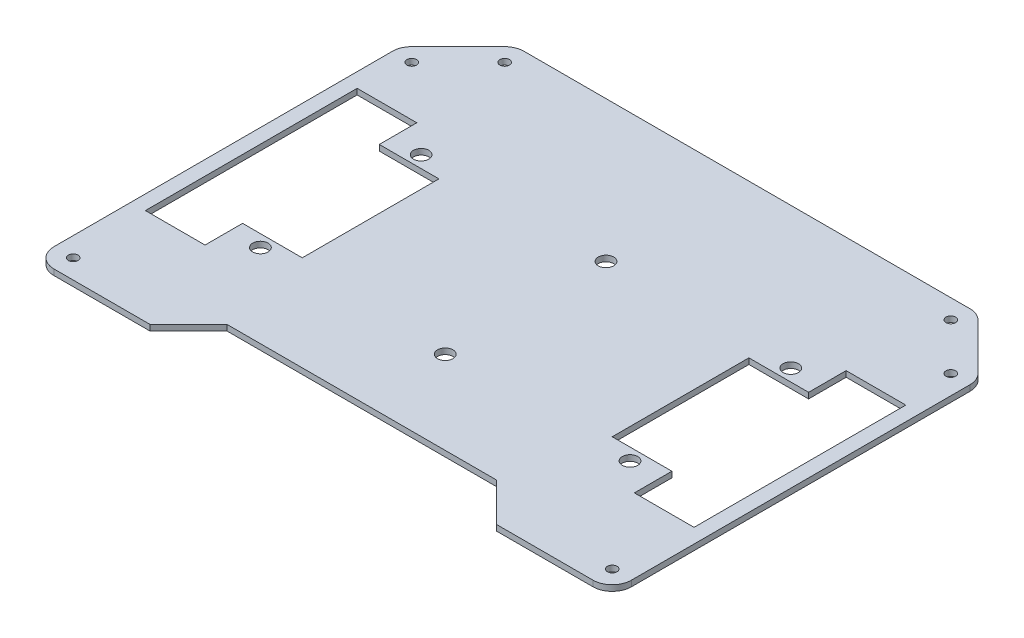
SolidWorks part; units mm, degrees
ref_plane "Face" through (0, 0, 0) normal (0, 0, 1) x (1, 0, 0)
ref_plane "Dessus" through (0, 0, 0) normal (0, 1, 0) x (1, 0, 0)
ref_plane "Droite" through (0, 0, 0) normal (1, 0, 0) x (0, 0, -1)
sketch "Esquisse1" plane through (0, 0, 0) normal (0, 1, 0) x (1, 0, 0)
  line L0 (-150, -105) -> (150, -105)
  line L1 (-150, 0) -> (-150, -105)
  line L2 (0, 115) -> (0, -105) construction
  line L3 (-150, 0) -> (-150, 85)
  line L4 (-150, 85) -> (-120, 115)
  line L5 (-120, 115) -> (120, 115)
  line L6 (150, 0) -> (150, -105)
  line L7 (-142.5, 55) -> (-142.5, -55)
  line L8 (-111.5, -55) -> (-142.5, -55)
  line L9 (-111.5, -35.5) -> (-111.5, -55)
  line L10 (-80.5, -35.5) -> (-111.5, -35.5)
  line L11 (-80.5, -35.5) -> (-80.5, 35.5)
  line L12 (-80.5, 35.5) -> (-111.5, 35.5)
  line L13 (-111.5, 35.5) -> (-111.5, 55)
  line L14 (-111.5, 55) -> (-142.5, 55)
  line L15 (111.5, 55) -> (142.5, 55)
  line L16 (-150, 0) -> (150, 0) construction
  line L17 (111.5, 35.5) -> (111.5, 55)
  line L18 (80.5, 35.5) -> (111.5, 35.5)
  line L19 (80.5, -35.5) -> (80.5, 35.5)
  line L20 (80.5, -35.5) -> (111.5, -35.5)
  line L21 (111.5, -35.5) -> (111.5, -55)
  line L22 (111.5, -55) -> (142.5, -55)
  line L23 (142.5, 55) -> (142.5, -55)
  line L24 (150, 85) -> (120, 115)
  line L25 (150, 0) -> (150, 85)
  line L26 (-96, 41.75) -> (0, 41.75) construction
  circle A0 centre (0, 41.75) radius 4
  circle A1 centre (-96, 41.75) radius 4
  circle A2 centre (0, -41.75) radius 4
  circle A3 centre (-96, -41.75) radius 4
  circle A4 centre (96, -41.75) radius 4
  circle A5 centre (96, 41.75) radius 4
  point P2 (0, 0)
  point P15 (-142.5, 0)
  point P22 (-80.5, 0)
  point P30 (80.5, 0)
  point P31 (142.5, 0)
  dimension "D12" = 8
  dimension "D2" = 50
  dimension "D3" = 45
  dimension "D4" = 110
  dimension "D5" = 31
  dimension "D6" = 71
  dimension "D7" = 161
  dimension "D8" = 285
  dimension "D9" = 30
  dimension "D10" = 220
  dimension "D11" = 300
  dimension "D13" = 96
  dimension "D14" = 41.75
extrude "Extrusion1" add sketch "Esquisse1" along normal blind 3
fillet "Congé2" radius 10 6 edges at (-150, 1.5, -85) (-120, 1.5, -115) (120, 1.5, -115) (150, 1.5, -85) (150, 1.5, 105) (-150, 1.5, 105)
sketch "Esquisse3" plane through (0, 3, 0) normal (0, 1, 0) x (1, 0, 0)
  line L3 (0, -105) -> (0, 115) construction
  line L4 (-140, -105) -> (140, -105) construction
  line L5 (115.8579, 115) -> (-115.8579, 115) construction
  circle A0 centre (-140, -95) radius 2.5
  circle A1 centre (-140, 80.8579) radius 2.5
  circle A2 centre (-115.8579, 105) radius 2.5
  circle A3 centre (140, -95) radius 2.5
  circle A4 centre (140, 80.8579) radius 2.5
  circle A5 centre (115.8579, 105) radius 2.5
  arc A6 (-150, -95) -> (-140, -105) centre (-140, -95) ccw construction
  arc A7 (-147.0711, 87.9289) -> (-150, 80.8579) centre (-140, 80.8579) ccw construction
  arc A8 (-115.8579, 115) -> (-122.9289, 112.0711) centre (-115.8579, 105) ccw construction
  dimension "D2" = 5
extrude "Extrusion2" cut sketch "Esquisse3" against normal up to next
sketch "Esquisse4" plane through (0, 3, 0) normal (0, 1, 0) x (1, 0, 0)
  line L0 (0, -105) -> (0, 115) construction
  line L1 (-140, -105) -> (140, -105) construction
  line L2 (115.8579, 115) -> (-115.8579, 115) construction
  line L3 (-90, -105) -> (-70, -85)
  line L4 (-70, -85) -> (70, -85)
  line L5 (-90, -105) -> (90, -105)
  line L6 (90, -105) -> (70, -85)
  point P10 (0, -85)
  dimension "D1" = 45
  dimension "D2" = 70
  dimension "D3" = 20
extrude "Extrusion3" cut sketch "Esquisse4" against normal up to next
